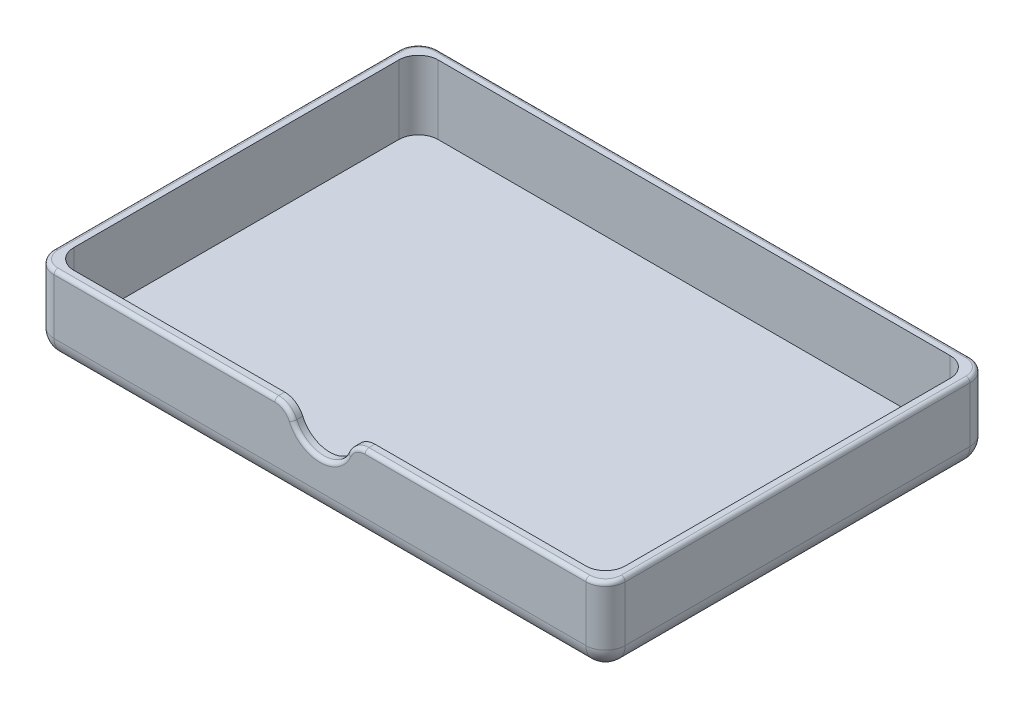
SolidWorks part; units mm, degrees
ref_plane "Front Plane" through (0, 0, 0) normal (0, 0, 1) x (1, 0, 0)
ref_plane "Top Plane" through (0, 0, 0) normal (0, 1, 0) x (1, 0, 0)
ref_plane "Right Plane" through (0, 0, 0) normal (1, 0, 0) x (0, 0, -1)
sketch "Sketch1" plane through (0, 0, 0) normal (0, 0, 1) x (1, 0, 0)
  line L0 (-145, -20) -> (145, -20)
  line L1 (145, -20) -> (145, 20)
  line L2 (145, 20) -> (-145, 20)
  line L3 (-145, 20) -> (-145, -20)
  arc A0 (15, 20) -> (-15, 20) centre (0, 20) cw
extrude "Boss-Extrude1" add sketch "Sketch1" against normal blind 5 contours L2 A0 L3 L0 L1
sketch "Sketch2" plane through (0, 0, -5) normal (0, 0, -1) x (-1, 0, 0)
  line L0 (-19.3649, 15) -> (-140, 15)
  line L1 (-140, 20) -> (-140, -15)
  line L2 (-140, -15) -> (140, -15)
  line L3 (140, -15) -> (140, 20)
  line L4 (140, 15) -> (19.3649, 15)
  line L5 (-15, 20) -> (-145, 20)
  line L6 (-145, 20) -> (-145, -20)
  line L7 (-145, -20) -> (145, -20)
  line L8 (145, -20) -> (145, 20)
  line L9 (145, 20) -> (15, 20)
  line L10 (-15, 20) -> (-145, 20)
  line L11 (-145, 20) -> (-145, -20)
  line L12 (-145, -20) -> (145, -20)
  line L13 (145, -20) -> (145, 20)
  line L14 (145, 20) -> (15, 20)
  line L15 (-140, 15) -> (-140, -15) construction
  line L16 (140, -15) -> (140, 15) construction
  arc A0 (-19.3649, 15) -> (19.3649, 15) centre (0, 20) ccw
  arc A1 (-15, 20) -> (15, 20) centre (0, 20) ccw
  arc A2 (-15, 20) -> (15, 20) centre (0, 20) ccw
  line M13 (-15, 20) -> (-145, 20)
  line M14 (-145, 20) -> (-145, -20)
  line M15 (-145, -20) -> (145, -20)
  line M16 (145, -20) -> (145, 20)
  line M17 (145, 20) -> (15, 20)
  dimension "D1" = 0
  dimension "D2" = 5
extrude "Boss-Extrude2" add sketch "Sketch2" along normal blind 185 contours L3 L2 L1 M13 M14 M15 M16 M17
sketch "Sketch3" plane through (0, 0, -190) normal (0, 0, -1) x (-1, 0, 0)
  line L0 (140, 20) -> (140, -15) construction
  line L1 (140, -15) -> (-140, -15) construction
  line L2 (-140, -15) -> (-140, 20) construction
  line L3 (-140, 20) -> (-145, 20) construction
  line L4 (-145, 20) -> (-145, -20) construction
  line L5 (-145, -20) -> (145, -20) construction
  line L6 (145, -20) -> (145, 20) construction
  line L7 (145, 20) -> (140, 20) construction
  line L8 (-140, -15) -> (140, -15) construction
  line L9 (140, -15) -> (140, 20) construction
  line L10 (140, 20) -> (15, 20) construction
  line L11 (-15, 20) -> (-140, 20) construction
  line L12 (-140, 20) -> (-140, -15) construction
  line L13 (140, 20) -> (140, -15)
  line L14 (140, -15) -> (-140, -15)
  line L15 (-140, -15) -> (-140, 20)
  line L16 (-140, 20) -> (-145, 20)
  line L17 (-145, 20) -> (-145, -20)
  line L18 (-145, -20) -> (145, -20)
  line L19 (145, -20) -> (145, 20)
  line L20 (145, 20) -> (140, 20)
  line L21 (-140, -15) -> (140, -15)
  line L22 (140, -15) -> (140, 20)
  line L23 (140, 20) -> (15, 20)
  line L24 (15, 20) -> (-140, 20)
  line L25 (-140, 20) -> (-140, -15)
  arc A0 (-15, 20) -> (15, 20) centre (0, 20) ccw construction
  arc A1 (-15, 20) -> (15, 20) centre (0, 20) ccw
  line M1 (140, 20) -> (140, -15)
  line M2 (140, -15) -> (-140, -15)
  line M3 (-140, -15) -> (-140, 20)
  line M4 (-140, 20) -> (-145, 20)
  line M5 (-145, 20) -> (-145, -20)
  line M6 (-145, -20) -> (145, -20)
  line M7 (145, -20) -> (145, 20)
  line M8 (145, 20) -> (140, 20)
extrude "Boss-Extrude3" add sketch "Sketch3" along normal blind 5 contours A1 L24 L23 M3 M2 M1 | L24 A1 | M8 M1 M2 M3 M4 M5 M6 M7
fillet "Fillet1" radius 10 14 edges at (-145, -20, -97.5) (145, -20, -97.5) (0, -20, 0) (-145, 0, 0) (145, 0, 0) (145, 0, -195) (-145, 0, -195) (-15, 20, -2.5) (15, 20, -2.5) (0, -20, -195) (140, 2.5, -5) (140, 2.5, -190) (-140, 2.5, -5) (-140, 2.5, -190)
fillet "Fillet2" radius 2 12 edges at (-142.0711, 20, -192.0711) (0, 20, -195) (142.0711, 20, -192.0711) (145, 20, -97.5) (142.0711, 20, -2.9289) (78.9564, 20, 0) (17.4357, 18.3666, 0) (0, 5, 0) (-17.4357, 18.3666, 0) (-78.9564, 20, 0) (-142.0711, 20, -2.9289) (-145, 20, -97.5)
sketch "Sketch4" plane through (0, 20, 0) normal (0, 1, 0) x (1, 0, 0)
  line L0 (145, 195) -> (-145, 195) construction
  line L1 (-145, 195) -> (-145, 0) construction
  line L2 (-145, 0) -> (145, 0) construction
  line L3 (145, 0) -> (145, 195) construction
  line L4 (-135, 185) -> (-135, 10)
  line L5 (135, 185) -> (-135, 185)
  line L6 (135, 10) -> (135, 185)
  line L7 (-135, 10) -> (135, 10)
  line L8 (-135, 185) -> (-135, 10) construction
  line L9 (135, 185) -> (-135, 185) construction
  line L10 (135, 10) -> (135, 185) construction
  line L11 (-135, 10) -> (135, 10) construction
  dimension "D1" = 0
  dimension "D2" = 10
sketch "Sketch5" plane through (145, 0, 0) normal (1, 0, 0) x (0, 0, -1)
  line L0 (0, 20) -> (0, -20) construction
  line L1 (0, 20) -> (195, 20) construction
  line L2 (195, 20) -> (0, 20) construction
